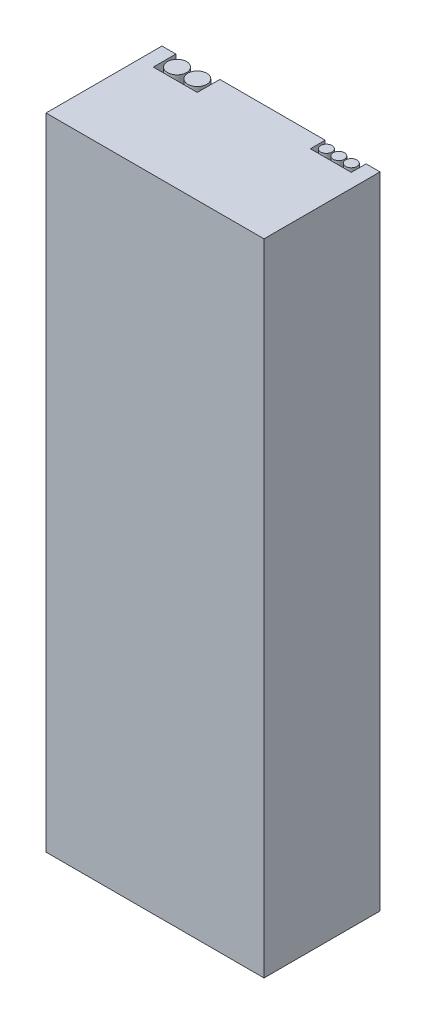
SolidWorks part; units mm, degrees
ref_plane "Front Plane" through (0, 0, 0) normal (0, 0, 1) x (1, 0, 0)
ref_plane "Top Plane" through (0, 0, 0) normal (0, 1, 0) x (1, 0, 0)
ref_plane "Right Plane" through (0, 0, 0) normal (1, 0, 0) x (0, 0, -1)
sketch "Sketch1" plane through (0, 0, 0) normal (0, 1, 0) x (1, 0, 0)
  line L1 (0, 0) -> (47, 0)
  line L2 (0, 0) -> (0, 25)
  line L3 (0, 25) -> (47, 25)
  line L4 (47, 0) -> (47, 25)
  dimension "D1" = 47
  dimension "D2" = 25
extrude "Boss-Extrude1" add sketch "Sketch1" along normal blind 138
sketch "Sketch2" plane through (0, 138, 0) normal (0, 1, 0) x (1, 0, 0)
  line L1 (47, 25) -> (0, 25) construction
  line L2 (3, 25) -> (12.48, 25)
  line L3 (3, 25) -> (3, 20.135)
  line L4 (12.48, 25) -> (12.48, 20.135)
  line L5 (3, 20.135) -> (12.48, 20.135)
  line L6 (0, 25) -> (0, 0) construction
  line L7 (44, 25) -> (35.18, 25)
  line L8 (44, 25) -> (44, 21.81)
  line L9 (35.18, 25) -> (35.18, 21.81)
  line L10 (44, 21.81) -> (35.18, 21.81)
  line L11 (47, 0) -> (47, 25) construction
  circle A0 centre (5.5575, 22.6925) radius 2.0575
  circle A1 centre (9.9225, 22.6925) radius 2.0575
  circle A2 centre (36.9, 23.53) radius 1.22
  circle A3 centre (39.59, 23.53) radius 1.22
  circle A4 centre (42.28, 23.53) radius 1.22
  dimension "D1" = 4.115
  dimension "D3" = 0.5
  dimension "D4" = 0.5
  dimension "D6" = 0.25
  dimension "D7" = 0.25
  dimension "D8" = 0.25
  dimension "D9" = 0.25
  dimension "D10" = 0.25
  dimension "D11" = 0.5
  dimension "D13" = 0.5
  dimension "D15" = 2.44
  dimension "D2" = 0.5
  dimension "D5" = 3
  dimension "D12" = 0.5
  dimension "D14" = 3
extrude "Cut-Extrude1" cut sketch "Sketch2" against normal blind 7 contours L4 L5 L3 L2 | A0 | A1 | L10 L9 L7 L8 | A2 | A3 | A4
